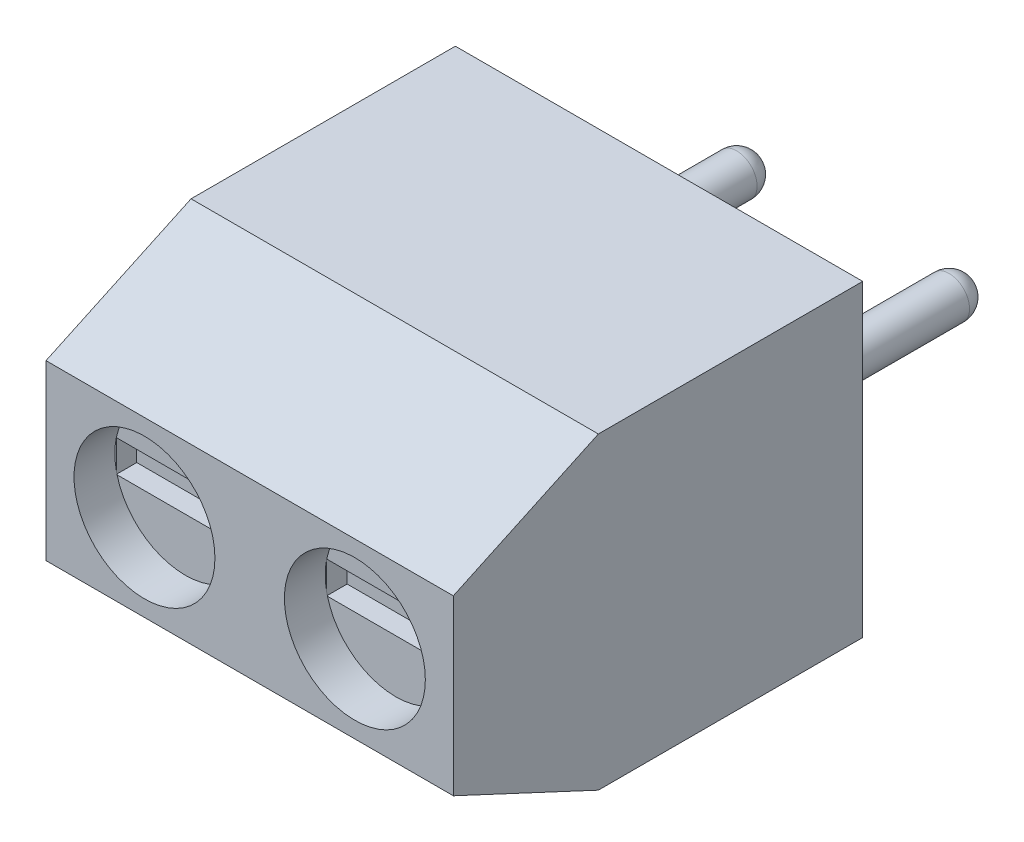
SolidWorks part; units mm, degrees
ref_plane "Face" through (0, 0, 0) normal (0, 0, 1) x (1, 0, 0)
ref_plane "Dessus" through (0, 0, 0) normal (0, 1, 0) x (1, 0, 0)
ref_plane "Droite" through (0, 0, 0) normal (1, 0, 0) x (0, 0, -1)
sketch "Esquisse1" plane through (0, 0, 0) normal (0, 0, 1) x (1, 0, 0)
  line L1 (0, 0) -> (9.97, 0)
  line L2 (0, 0) -> (0, 7.55)
  line L3 (0, 7.55) -> (9.97, 7.55)
  line L4 (9.97, 0) -> (9.97, 7.55)
  dimension "D1" = 9.97
  dimension "D2" = 7.55
extrude "Extrusion1" add sketch "Esquisse1" along normal blind 10.02
chamfer "Chanfrein1" distance 3.55 angle 25 2 edges at (4.985, 7.55, 10.02) (4.985, 0, 10.02)
sketch "Esquisse2" plane through (0, 0, 10.02) normal (0, 0, 1) x (1, 0, 0)
  line L0 (0, 3.775) -> (9.97, 3.775) construction
  line L1 (0, 5.8946) -> (0, 1.6554) construction
  line L2 (9.97, 1.6554) -> (9.97, 5.8946) construction
  line L3 (4.985, 5.8946) -> (4.985, 1.6554) construction
  line L4 (9.97, 5.8946) -> (0, 5.8946) construction
  line L5 (0, 1.6554) -> (9.97, 1.6554) construction
  circle A0 centre (2.4101, 3.775) radius 1.725
  circle A1 centre (7.5599, 3.775) radius 1.725
  dimension "D1" = 3.45
extrude "Enlèv. mat.-Extru.1" cut sketch "Esquisse2" against normal blind 1
sketch "Esquisse3" plane through (0, 0, 0) normal (0, -1, 0) x (1, 0, 0)
  line L0 (4.985, 6.47) -> (4.985, 0) construction
  line L1 (9.97, 6.47) -> (0, 6.47) construction
  line L2 (0, 0) -> (9.97, 0) construction
  line L4 (9.435, 5.8) -> (5.435, 5.8)
  line L5 (9.435, 5.8) -> (9.435, 0.8)
  line L6 (9.435, 0.8) -> (5.435, 0.8)
  line L7 (5.435, 5.8) -> (5.435, 0.8)
  line L8 (4.535, 5.8) -> (0.535, 5.8)
  line L9 (4.535, 5.8) -> (4.535, 0.8)
  line L10 (4.535, 0.8) -> (0.535, 0.8)
  line L11 (0.535, 5.8) -> (0.535, 0.8)
  dimension "D1" = 5
  dimension "D2" = 4
  dimension "D3" = 0.8
  dimension "D4" = 0.9
extrude "Enlèv. mat.-Extru.2" cut sketch "Esquisse3" against normal blind 1.6
sketch "Esquisse4" plane through (0, 1.6, 0) normal (0, -1, 0) x (1, 0, 0)
  line L0 (9.97, 3.235) -> (0, 3.235) construction
  line L1 (9.97, 6.47) -> (9.97, 0) construction
  line L2 (0, 6.47) -> (0, 0) construction
  line L3 (7.435, 5.8) -> (7.435, 0.8) construction
  line L4 (9.435, 5.8) -> (5.435, 5.8) construction
  line L5 (5.435, 0.8) -> (9.435, 0.8) construction
  line L6 (2.535, 5.8) -> (2.535, 0.8) construction
  line L7 (4.535, 5.8) -> (0.535, 5.8) construction
  line L8 (0.535, 0.8) -> (4.535, 0.8) construction
  circle A0 centre (7.435, 3.235) radius 1.675
  circle A1 centre (2.535, 3.235) radius 1.675
  dimension "D1" = 3.35
extrude "Enlèv. mat.-Extru.3" cut sketch "Esquisse4" against normal blind 1.6
sketch "Esquisse5" plane through (0, 0, 0) normal (0, 0, -1) x (-1, 0, 0)
  line L0 (-9.97, 3.775) -> (0, 3.775) construction
  line L1 (-9.97, 0) -> (-9.97, 7.55) construction
  line L2 (0, 7.55) -> (0, 0) construction
  line L3 (-4.985, 7.55) -> (-4.985, 0) construction
  line L4 (-9.97, 7.55) -> (0, 7.55) construction
  line L5 (0, 0) -> (-9.97, 0) construction
  circle A0 centre (-7.585, 3.775) radius 0.5
  circle A1 centre (-2.385, 3.775) radius 0.5
  dimension "D1" = 1
  dimension "D2" = 5.2
extrude "Extrusion2" add sketch "Esquisse5" along normal blind 5
fillet "Congé1" radius 0.5 2 edges at (7.085, 3.775, -5) (1.885, 3.775, -5)
sketch "Esquisse7" plane through (0, 0, 9.02) normal (0, 0, 1) x (1, 0, 0)
  line L1 (0.721, 4.1248) -> (4.0806, 4.1248)
  line L2 (0.721, 4.1248) -> (0.721, 3.3447)
  line L3 (0.721, 3.3447) -> (4.0806, 3.3447)
  line L4 (4.0806, 4.1248) -> (4.0806, 3.3447)
  line L5 (5.8707, 4.1248) -> (9.2304, 4.1248)
  line L6 (5.8707, 4.1248) -> (5.8707, 3.3447)
  line L7 (5.8707, 3.3447) -> (9.2304, 3.3447)
  line L8 (9.2304, 4.1248) -> (9.2304, 3.3447)
  circle A0 centre (2.4101, 3.775) radius 1.725 construction
  circle A1 centre (7.5599, 3.775) radius 1.725 construction
extrude "Enlèv. mat.-Extru.4" cut sketch "Esquisse7" against normal blind 0.5
sketch "Esquisse8" plane through (0, 3.2, 0) normal (0, -1, 0) x (1, 0, 0)
  line L1 (0.9436, 3.7576) -> (4.1396, 3.7576)
  line L2 (0.9436, 3.7576) -> (0.9436, 2.7545)
  line L3 (0.9436, 2.7545) -> (4.1396, 2.7545)
  line L4 (4.1396, 3.7576) -> (4.1396, 2.7545)
  line L5 (5.8436, 3.7576) -> (9.0396, 3.7576)
  line L6 (5.8436, 3.7576) -> (5.8436, 2.7545)
  line L7 (5.8436, 2.7545) -> (9.0396, 2.7545)
  line L8 (9.0396, 3.7576) -> (9.0396, 2.7545)
  circle A0 centre (2.535, 3.235) radius 1.675 construction
  circle A1 centre (7.435, 3.235) radius 1.675 construction
extrude "Enlèv. mat.-Extru.5" cut sketch "Esquisse8" against normal blind 0.5
